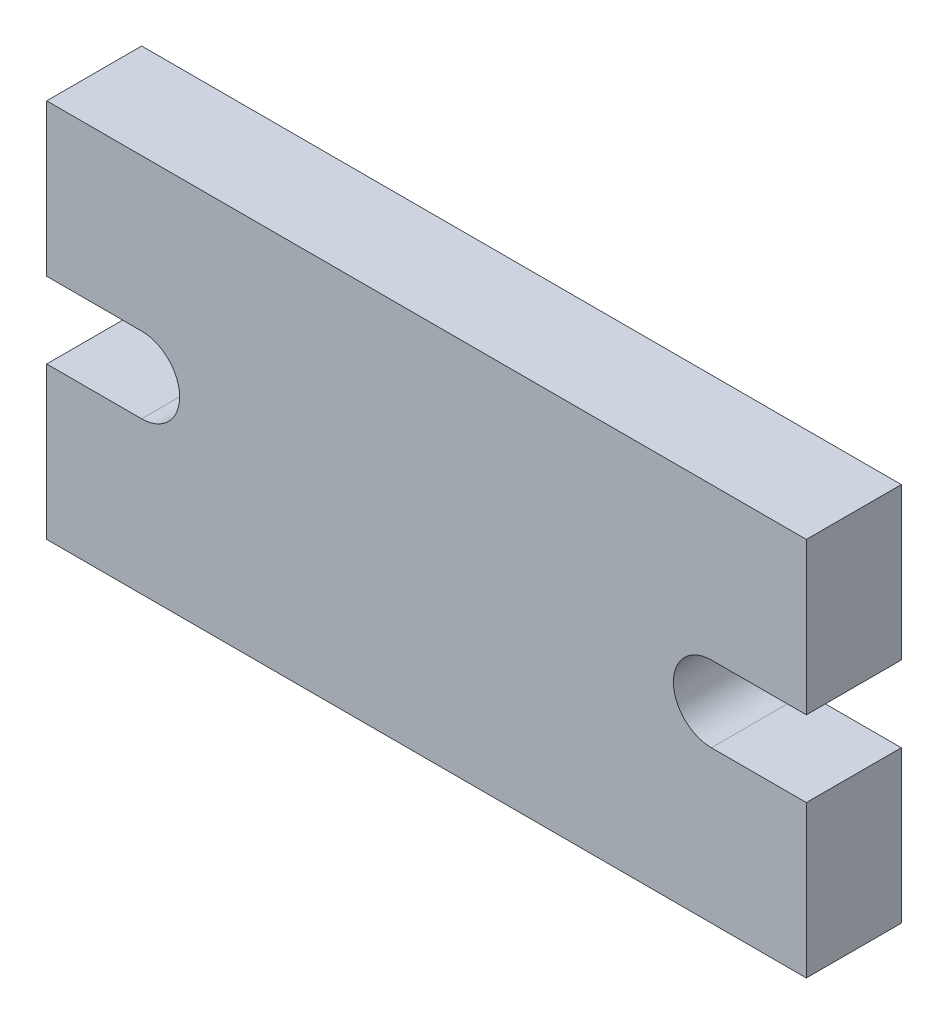
SolidWorks part; units mm, degrees
ref_plane "Front Plane" through (0, 0, 0) normal (0, 0, 1) x (1, 0, 0)
ref_plane "Top Plane" through (0, 0, 0) normal (0, 1, 0) x (1, 0, 0)
ref_plane "Right Plane" through (0, 0, 0) normal (1, 0, 0) x (0, 0, -1)
sketch "Sketch1" plane through (0, 0, 0) normal (0, 0, 1) x (1, 0, 0)
  line L0 (19.6154, -0.3654) -> (19.6154, -8.3654)
  line L1 (-20.3846, 11.6346) -> (19.6154, 11.6346)
  line L2 (-20.3846, 11.6346) -> (-20.3846, 3.6346)
  line L3 (-20.3846, -8.3654) -> (19.6154, -8.3654)
  line L4 (19.6154, 11.6346) -> (19.6154, 3.6346)
  line L5 (-20.3846, 3.6346) -> (-15.3846, 3.6346)
  line L6 (19.6154, -0.3654) -> (14.6154, -0.3654)
  line L7 (-20.3846, -0.3654) -> (-15.3846, -0.3654)
  line L8 (19.6154, 3.6346) -> (14.6154, 3.6346)
  line L9 (-20.3846, -0.3654) -> (-20.3846, -8.3654)
  arc A0 (-15.3846, -0.3654) -> (-15.3846, 3.6346) centre (-15.3846, 1.6346) ccw
  arc A1 (14.6154, -0.3654) -> (14.6154, 3.6346) centre (14.6154, 1.6346) cw
  point P4 (-20.3846, 1.6346)
  point P6 (0, 0)
  point P10 (0, 0)
  dimension "D1" = 40
  dimension "D2" = 20
  dimension "D3" = 5
  dimension "D4" = 4
  dimension "D5" = 2
extrude "Boss-Extrude1" add sketch "Sketch1" along normal blind 5
